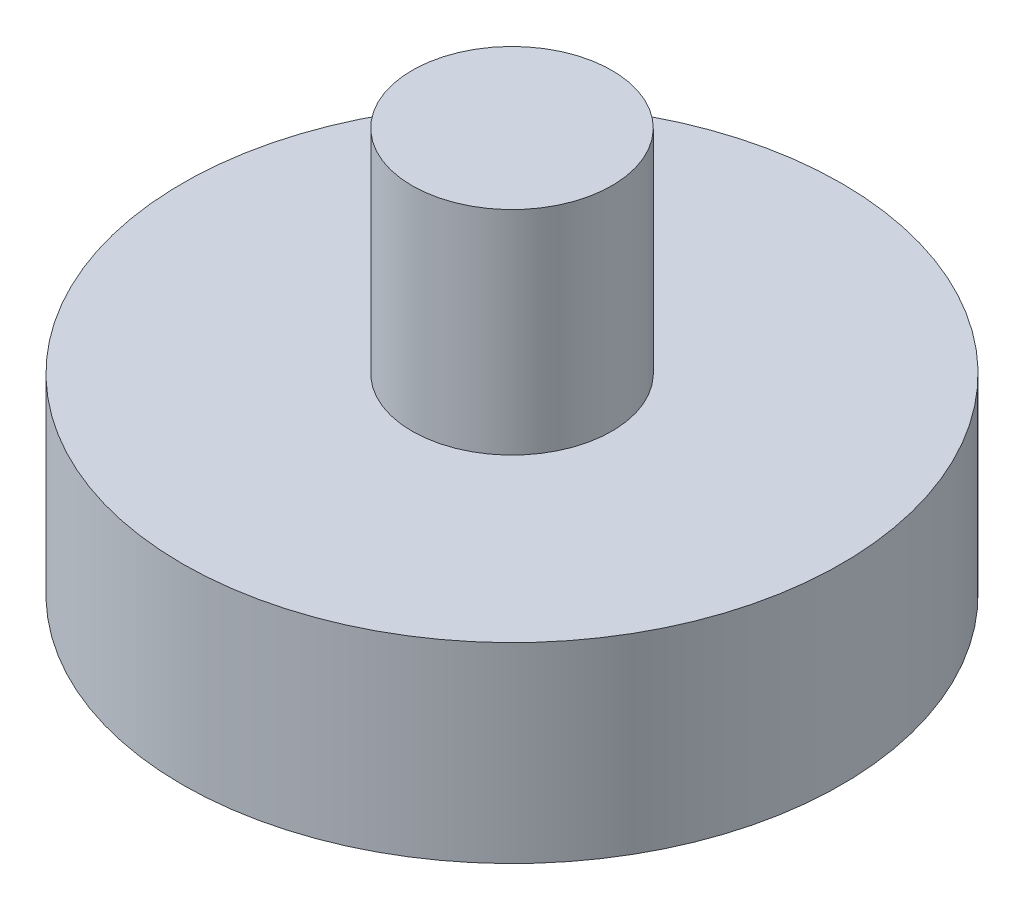
SolidWorks part; units mm, degrees
ref_plane "Ön Düzlem" through (0, 0, 0) normal (0, 0, 1) x (1, 0, 0)
ref_plane "Üst Düzlem" through (0, 0, 0) normal (0, 1, 0) x (1, 0, 0)
ref_plane "Sağ Düzlem" through (0, 0, 0) normal (1, 0, 0) x (0, 0, -1)
sketch "Çizim1" plane through (0, 0, 0) normal (0, 1, 0) x (1, 0, 0)
  circle A0 centre (0, 0) radius 7.75
  dimension "D1" = 15.5
extrude "Yükseklik-Ekstrüzyon1" add sketch "Çizim1" along normal blind 4.5
sketch "Çizim2" plane through (0, 4.5, 0) normal (0, 1, 0) x (1, 0, 0)
  circle A0 centre (0, 0) radius 2.35
  dimension "D1" = 4.7
extrude "Yükseklik-Ekstrüzyon2" add sketch "Çizim2" along normal blind 5
sketch "Çizim3" plane through (0, 0, 0) normal (0, -1, 0) x (1, 0, 0)
  circle A0 centre (0, 0) radius 3.1
  dimension "D1" = 6.2
extrude "Kes-Ekstrüzyon1" cut sketch "Çizim3" against normal blind 3.5
